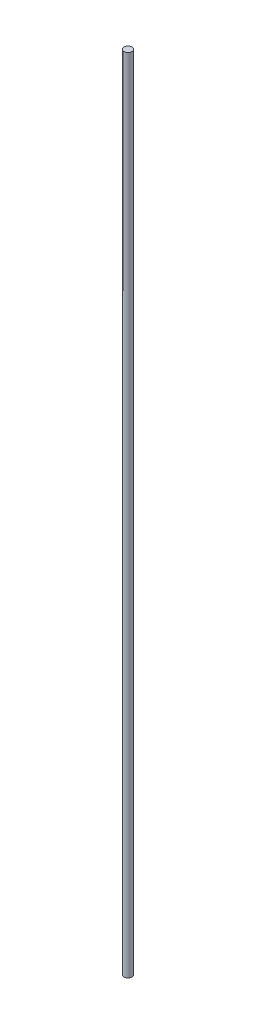
SolidWorks part; units mm, degrees
ref_plane "Front Plane" through (0, 0, 0) normal (0, 0, 1) x (1, 0, 0)
ref_plane "Top Plane" through (0, 0, 0) normal (0, 1, 0) x (1, 0, 0)
ref_plane "Right Plane" through (0, 0, 0) normal (1, 0, 0) x (0, 0, -1)
sketch "Sketch3" plane through (0, 0, 0) normal (0, 1, 0) x (1, 0, 0)
  circle A0 centre (0, 0) radius 12
  dimension "D1" = 24
extrude "Boss-Extrude1" add sketch "Sketch3" along normal blind 2400
